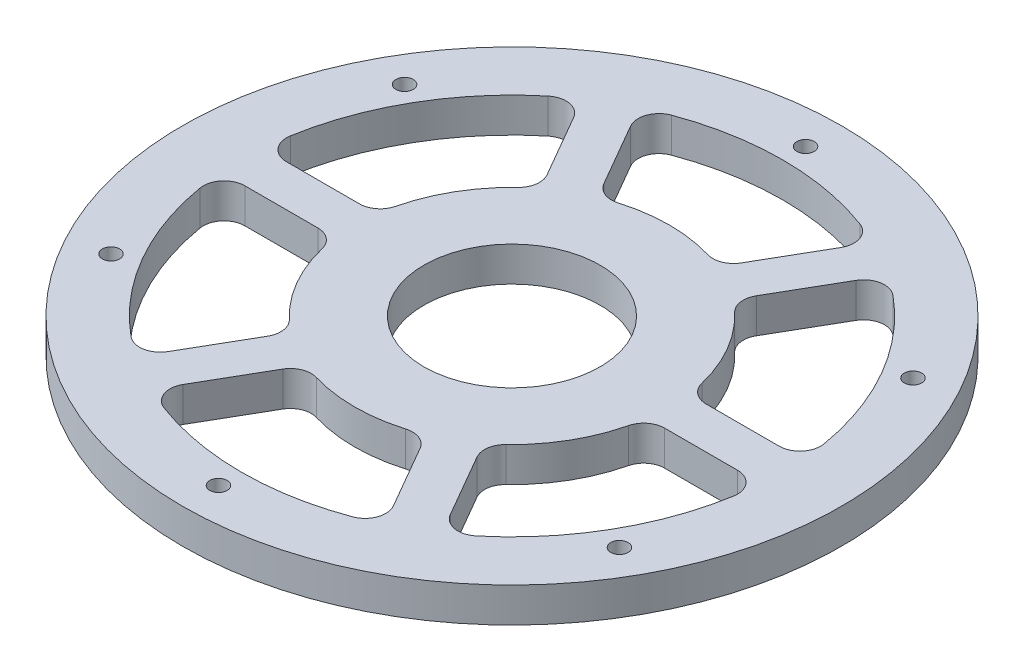
SolidWorks part; units mm, degrees
material "ABS"
ref_plane "Front Plane" through (0, 0, 0) normal (0, 0, 1) x (1, 0, 0)
ref_plane "Top Plane" through (0, 0, 0) normal (0, 1, 0) x (1, 0, 0)
ref_plane "Right Plane" through (0, 0, 0) normal (1, 0, 0) x (0, 0, -1)
sketch "Sketch1" plane through (0, 0, 0) normal (0, 1, 0) x (1, 0, 0)
  circle A0 centre (0, 0) radius 47.5
  dimension "D1" = 95
extrude "Boss-Extrude1" add sketch "Sketch1" along normal blind 5
sketch "Sketch2" plane through (0, 5, 0) normal (0, 1, 0) x (1, 0, 0)
  circle A0 centre (0, 0) radius 12.7
  dimension "D1" = 25.4
extrude "Cut-Extrude1" cut sketch "Sketch2" against normal through all
sketch "Sketch3" plane through (0, 5, 0) normal (0, 1, 0) x (1, 0, 0)
  circle A0 centre (0, 0) radius 42.31 construction
  circle A1 centre (0, 42.31) radius 1.25
  circle A2 centre (36.6415, 21.155) radius 1.25
  circle A3 centre (36.6415, -21.155) radius 1.25
  circle A4 centre (0, -42.31) radius 1.25
  circle A5 centre (-36.6415, -21.155) radius 1.25
  circle A6 centre (-36.6415, 21.155) radius 1.25
  point P17 (0, 0)
  dimension "D1" = 84.62
  dimension "D2" = 2.5
  dimension "D3" = 6
extrude "Cut-Extrude2" cut sketch "Sketch3" against normal blind 2.5
sketch "Sketch4" plane through (0, 5, 0) normal (0, 1, 0) x (1, 0, 0)
  line L0 (0, 0) -> (0, 39) construction
  line L1 (0, 0) -> (-19.5, 33.775) construction
  line L2 (-22.0403, 32.1749) -> (-13.8485, 17.9863)
  line L3 (-16.8441, 35.1749) -> (-8.6524, 20.9863)
  line L4 (16.8441, 35.1749) -> (8.6524, 20.9863)
  line L5 (22.0403, 32.1749) -> (13.8485, 17.9863)
  line L6 (38.8844, 3) -> (22.5009, 3)
  line L7 (38.8844, -3) -> (22.5009, -3)
  line L8 (22.0403, -32.1749) -> (13.8485, -17.9863)
  line L9 (16.8441, -35.1749) -> (8.6524, -20.9863)
  line L10 (-16.8441, -35.1749) -> (-8.6524, -20.9863)
  line L11 (-22.0403, -32.1749) -> (-13.8485, -17.9863)
  line L12 (-38.8844, -3) -> (-22.5009, -3)
  line L13 (-38.8844, 3) -> (-22.5009, 3)
  circle A0 centre (0, 0) radius 39
  circle A1 centre (0, 0) radius 22.7
  circle A2 centre (0, 0) radius 12.7 construction
  point P38 (0, 0)
  dimension "D1" = 10
  dimension "45" = 78
  dimension "D2" = 30
  dimension "D3" = 3
  dimension "D4" = 6
extrude "Cut-Extrude3" cut sketch "Sketch4" against normal through all contours A1 L2 A0 L13 | A1 L4 A0 L3 | A1 L6 A0 L5 | A1 L8 A0 L7 | A1 L10 A0 L9 | A1 L12 A0 L11
fillet "Fillet1" radius 3 24 edges at (-8.6524, 2.5, -20.9863) (-16.8441, 2.5, -35.1749) (8.6524, 2.5, -20.9863) (16.8441, 2.5, -35.1749) (22.5009, 2.5, -3) (38.8844, 2.5, -3) (22.0403, 2.5, -32.1749) (13.8485, 2.5, -17.9863) (13.8485, 2.5, 17.9863) (22.0403, 2.5, 32.1749) (22.5009, 2.5, 3) (38.8844, 2.5, 3) (-16.8441, 2.5, 35.1749) (16.8441, 2.5, 35.1749) (8.6524, 2.5, 20.9863) (-8.6524, 2.5, 20.9863) (-22.0403, 2.5, 32.1749) (-13.8485, 2.5, 17.9863) (-22.5009, 2.5, 3) (-38.8844, 2.5, 3) (-13.8485, 2.5, -17.9863) (-22.5009, 2.5, -3) (-38.8844, 2.5, -3) (-22.0403, 2.5, -32.1749)
